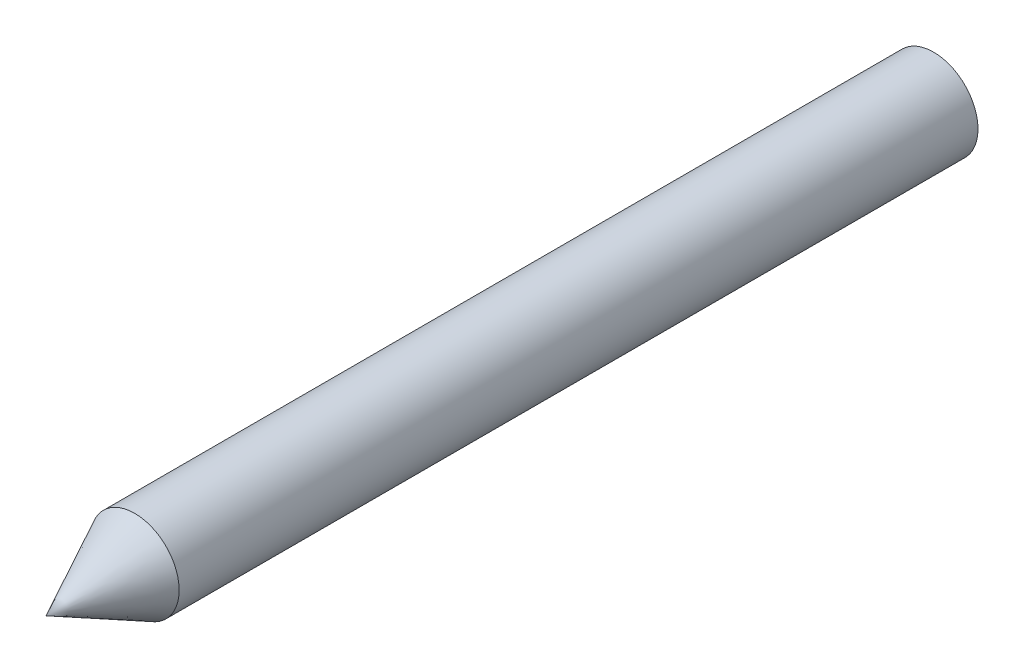
SolidWorks part; units mm, degrees
ref_plane "Front Plane" through (0, 0, 0) normal (0, 0, 1) x (1, 0, 0)
ref_plane "Top Plane" through (0, 0, 0) normal (0, 1, 0) x (1, 0, 0)
ref_plane "Right Plane" through (0, 0, 0) normal (1, 0, 0) x (0, 0, -1)
sketch "Sketch1" plane through (0, 0, 0) normal (0, 0, 1) x (1, 0, 0)
  circle A0 centre (0, 0) radius 25
  dimension "D1" = 50
extrude "Boss-Extrude1" add sketch "Sketch1" along normal blind 450
sketch "Sketch2" plane through (0, 0, 0) normal (0, 1, 0) x (1, 0, 0)
  line L0 (0, -450) -> (-25, -450)
  line L1 (0, -450) -> (0, -500)
  line L2 (-25, -450) -> (25, -450) construction
  line L3 (0, -500) -> (-25, -450)
  dimension "D1" = 50
revolve "Revolve1" add sketch "Sketch2" angle 360 about L1
